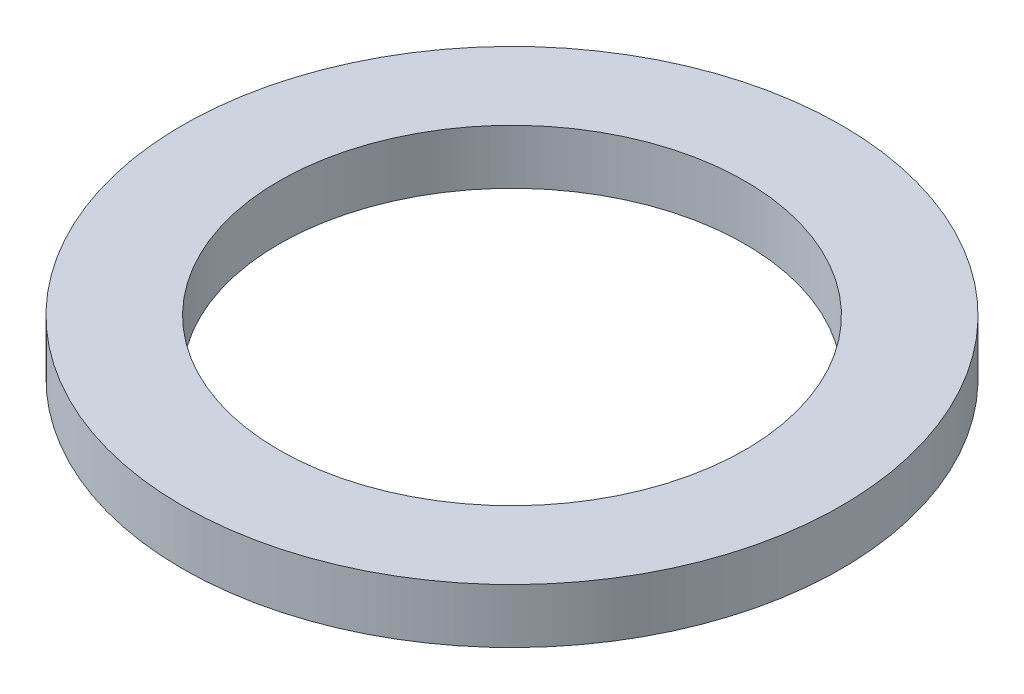
SolidWorks part; units mm, degrees
material "G10 Fiberglass"
ref_plane "Front Plane" through (0, 0, 0) normal (0, 0, 1) x (1, 0, 0)
ref_plane "Top Plane" through (0, 0, 0) normal (0, 1, 0) x (1, 0, 0)
ref_plane "Right Plane" through (0, 0, 0) normal (1, 0, 0) x (0, 0, -1)
sketch "Sketch1" plane through (0, 0, 0) normal (0, 0, 1) x (1, 0, 0)
  line L0 (0, 22.7096) -> (0, -29.6046) construction
  line L2 (27.1145, -6.35) -> (38.354, -6.35)
  line L3 (27.1145, -6.35) -> (27.1145, 0)
  line L4 (27.1145, 0) -> (38.354, 0)
  line L5 (38.354, -6.35) -> (38.354, 0)
  dimension "D2" = 6.35
  dimension "D3" = 27.1145
  dimension "D4" = 6.35
  dimension "D1" = 38.354
revolve "Revolve1" add sketch "Sketch1" angle 360 about L0
equation "\"D1@Sketch1\"=3.02/2"
equation "\"D4@Sketch1\"=\"D2@Sketch1\""
